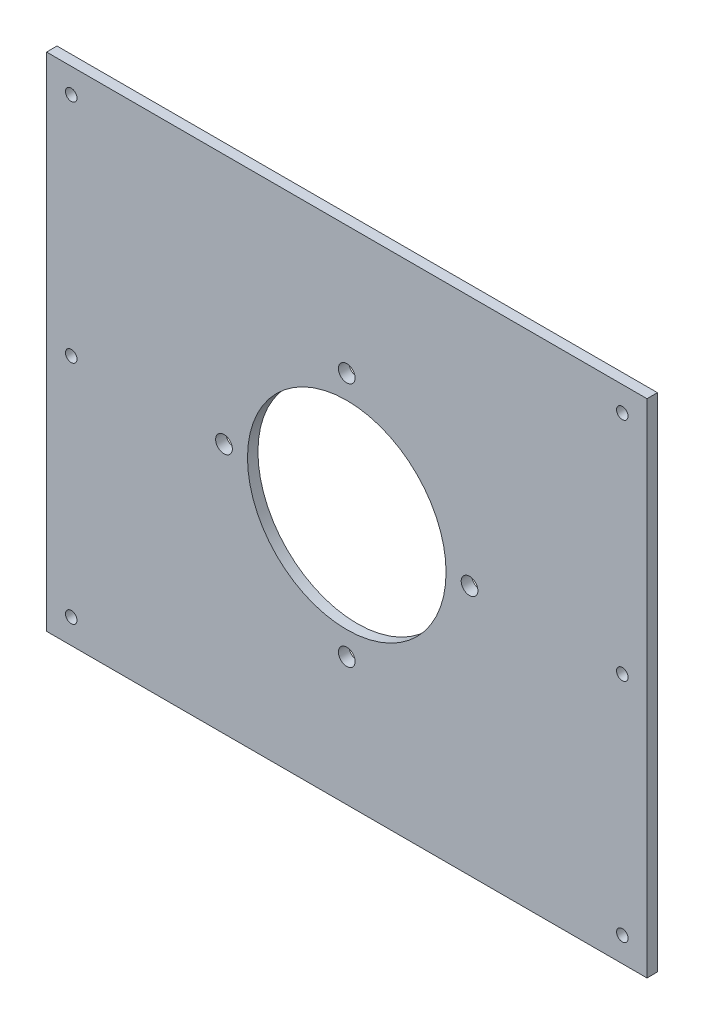
SolidWorks part; units mm, degrees
ref_plane "Front Plane" through (0, 0, 0) normal (0, 0, 1) x (1, 0, 0)
ref_plane "Top Plane" through (0, 0, 0) normal (0, 1, 0) x (1, 0, 0)
ref_plane "Right Plane" through (0, 0, 0) normal (1, 0, 0) x (0, 0, -1)
sketch "Sketch1" plane through (0, 0, 0) normal (0, 0, 1) x (1, 0, 0)
  line L0 (-80.2008, -94.5008) -> (284.5992, 210.2992) construction
  line L1 (-80.2008, -94.5008) -> (284.5992, -94.5008)
  line L2 (-80.2008, -94.5008) -> (-80.2008, 210.2992)
  line L3 (-80.2008, 210.2992) -> (284.5992, 210.2992)
  line L4 (284.5992, -94.5008) -> (284.5992, 210.2992)
  circle A0 centre (102.1992, 57.8992) radius 60.325
  circle A1 centre (102.1992, 57.8992) radius 74.6
  circle A2 centre (102.1992, 132.4992) radius 5.08
  circle A3 centre (27.5992, 57.8992) radius 5.08
  circle A4 centre (102.1992, -16.7008) radius 5.08
  circle A5 centre (176.7992, 57.8992) radius 5.08
  circle A6 centre (-65.2008, 195.2992) radius 3.5
  circle A7 centre (-65.2008, 57.8992) radius 3.5
  circle A8 centre (-65.2008, -79.5008) radius 3.5
  circle A9 centre (269.5992, 195.2992) radius 3.5
  circle A10 centre (269.5992, 57.8992) radius 3.5
  circle A11 centre (269.5992, -79.5008) radius 3.5
  point P11 (102.1992, 57.8992)
  dimension "D3" = 120.65
  dimension "D6" = 149.2
  dimension "D7" = 10.16
  dimension "D8" = 10.16
  dimension "D9" = 10.16
  dimension "D10" = 10.16
  dimension "D11" = 7
  dimension "D14" = 7
  dimension "D17" = 7
  dimension "D20" = 7
  dimension "D23" = 7
  dimension "D26" = 7
  dimension "D1" = 364.8
  dimension "D2" = 304.8
  dimension "D4" = 0
  dimension "D5" = 0
  dimension "D12" = 15
  dimension "D13" = 15
  dimension "D15" = 15
  dimension "D16" = 152.4
  dimension "D18" = 15
  dimension "D19" = 15
  dimension "D21" = 15
  dimension "D22" = 15
  dimension "D24" = 15
  dimension "D25" = 152.4
  dimension "D27" = 15
  dimension "D28" = 15
extrude "Boss-Extrude1" add sketch "Sketch1" along normal blind 6.35 contours L0 L1 L4 A9 A1 A5 A4 A8 A11 A10 | L2 L0 A8 A1 A3 A2 A9 L3 A6 A7 | A1 L0 A0 A2 A3 | L0 A1 A4 A5 A0
equation "\"D16@Sketch1\"=\"D2@Sketch1\"/2"
equation "\"D25@Sketch1\"=\"D2@Sketch1\"/2"
